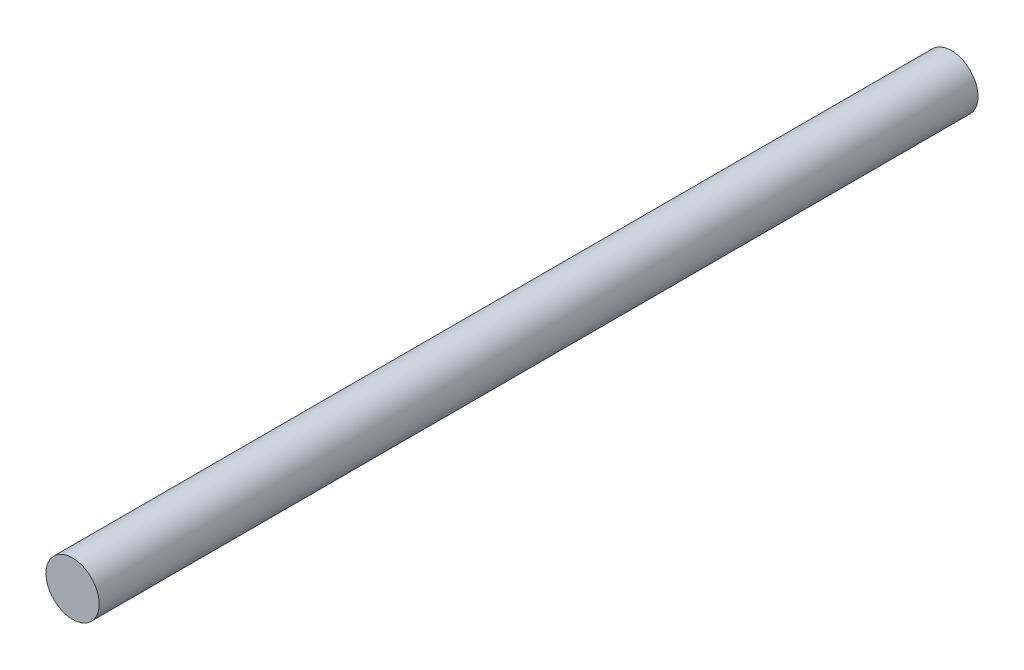
SolidWorks part; units mm, degrees
ref_plane "Front Plane" through (0, 0, 0) normal (0, 0, 1) x (1, 0, 0)
ref_plane "Top Plane" through (0, 0, 0) normal (0, 1, 0) x (1, 0, 0)
ref_plane "Right Plane" through (0, 0, 0) normal (1, 0, 0) x (0, 0, -1)
sketch "Sketch1" plane through (0, 0, 0) normal (0, 0, 1) x (1, 0, 0)
  circle A0 centre (0, 0) radius 13.8471
extrude "Boss-Extrude3" add sketch "Sketch1" along normal blind 457.2
